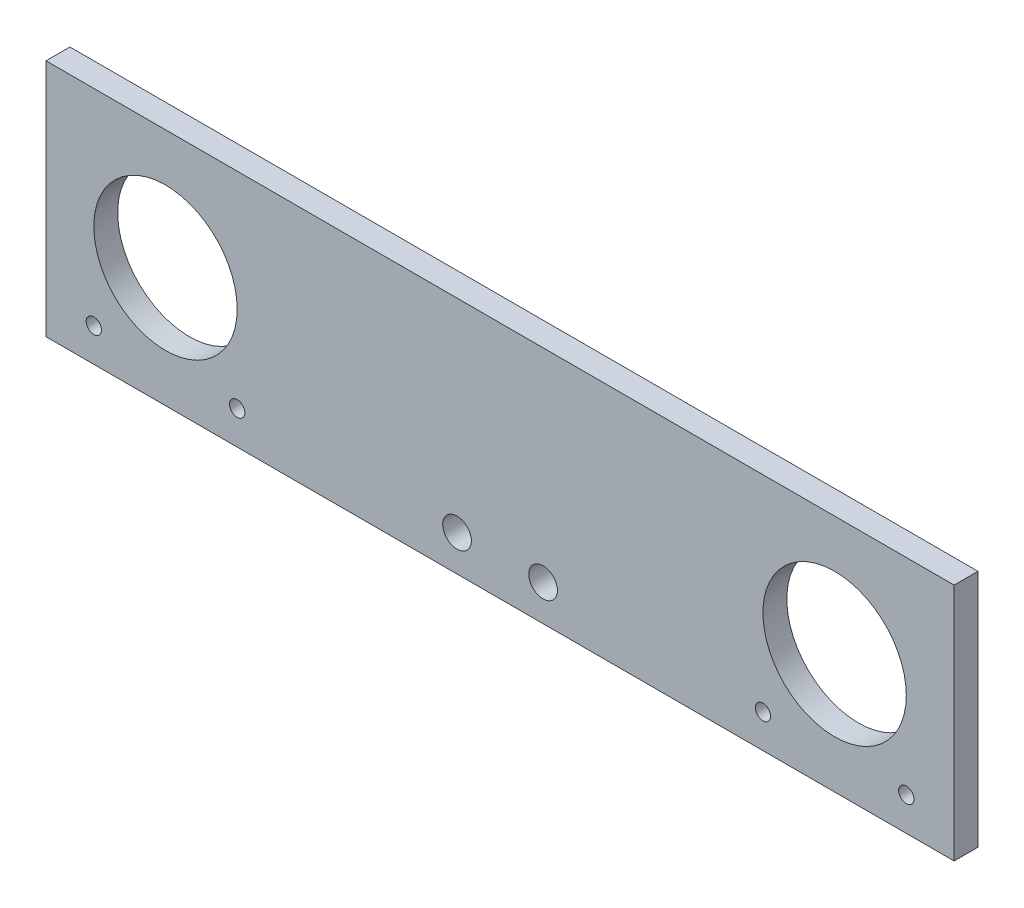
SolidWorks part; units mm, degrees
ref_plane "Front Plane" through (0, 0, 0) normal (0, 0, 1) x (1, 0, 0)
ref_plane "Top Plane" through (0, 0, 0) normal (0, 1, 0) x (1, 0, 0)
ref_plane "Right Plane" through (0, 0, 0) normal (1, 0, 0) x (0, 0, -1)
sketch "Sketch1" plane through (0, 0, 0) normal (0, 0, 1) x (1, 0, 0)
  line L1 (0, 0) -> (190, 0)
  line L2 (0, 0) -> (0, 50)
  line L3 (0, 50) -> (190, 50)
  line L4 (190, 0) -> (190, 50)
  circle A0 centre (25, 25) radius 15
  circle A1 centre (165, 25) radius 15
  circle A2 centre (40, 7) radius 1.6
  circle A3 centre (180, 7) radius 1.6
  circle A4 centre (150, 7) radius 1.6
  circle A5 centre (10, 7) radius 1.6
  circle A6 centre (86, 7.5) radius 3
  circle A7 centre (104, 7.5) radius 3
  point P5 (95, 25)
  dimension "D3" = 30
  dimension "D7" = 30
  dimension "D9" = 3.2
  dimension "D11" = 15
  dimension "D15" = 3.2
  dimension "D16" = 7
  dimension "D23" = 6
  dimension "D24" = 6
  dimension "D12" = 7
  dimension "D14" = 3.2
  dimension "D18" = 3.2
  dimension "D2" = 50
  dimension "D4" = 70
  dimension "D5" = 95
  dimension "D6" = 25
  dimension "D8" = 70
  dimension "D10" = 15
  dimension "D13" = 7
  dimension "D17" = 15
  dimension "D20" = 7
  dimension "D21" = 25
  dimension "D22" = 25
  dimension "D25" = 7.5
  dimension "D26" = 7.5
  dimension "D27" = 9
  dimension "D32" = 95
  dimension "D35" = 9
extrude "Boss-Extrude1" add sketch "Sketch1" along normal blind 5
sketch "Sketch3" plane through (0, 0, 5) normal (0, 0, 1) x (1, 0, 0)
  circle A0 centre (10, 7) radius 2.75
  circle A1 centre (40, 7) radius 2.75
  circle A2 centre (150, 7) radius 2.75
  circle A3 centre (180, 7) radius 2.75
  dimension "D1" = 5.5
extrude "Cut-Extrude1" [suppressed] cut sketch "Sketch3" against normal blind 1.5 contours A0 | A1 | A2 | A3
